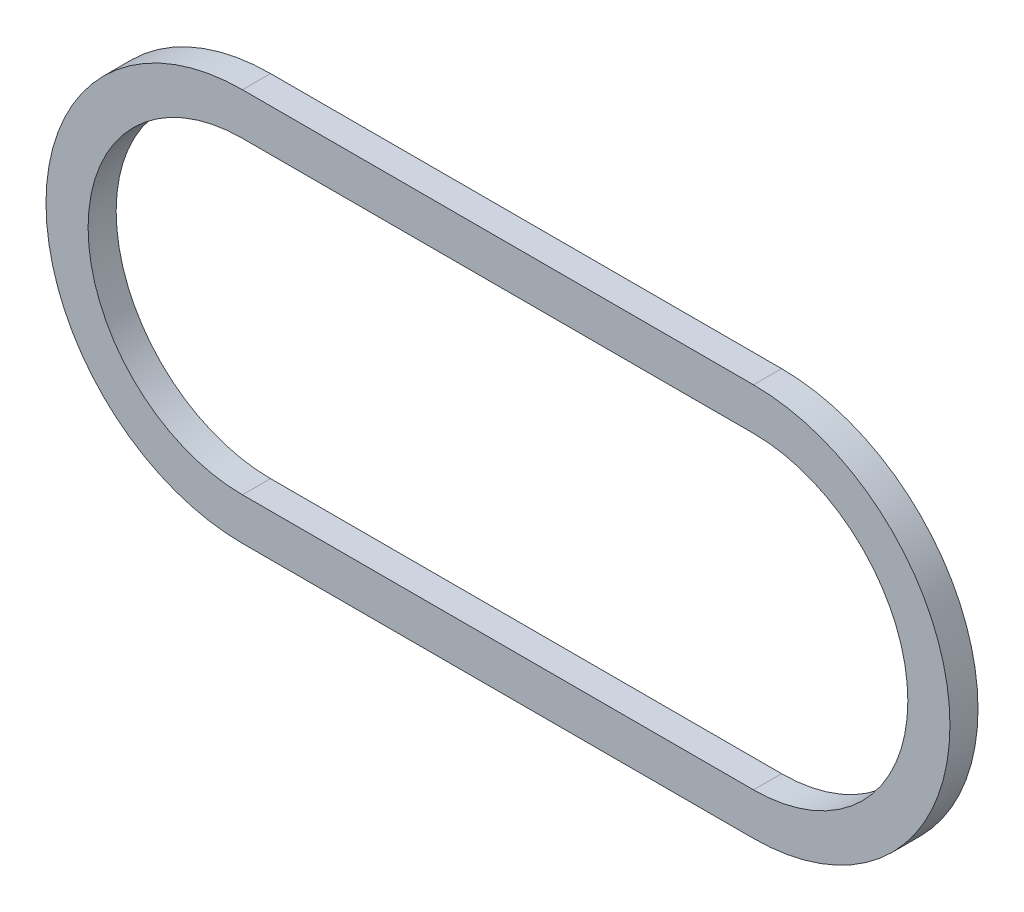
SolidWorks part; units mm, degrees
ref_plane "Front Plane" through (0, 0, 0) normal (0, 0, 1) x (1, 0, 0)
ref_plane "Top Plane" through (0, 0, 0) normal (0, 1, 0) x (1, 0, 0)
ref_plane "Right Plane" through (0, 0, 0) normal (1, 0, 0) x (0, 0, -1)
sketch "Sketch1" plane through (0, 0, 0) normal (0, 0, 1) x (1, 0, 0)
  line L0 (-18.21, 0) -> (18.21, 0) construction
  line L1 (-18.21, 11) -> (18.21, 11)
  line L2 (-18.21, -11) -> (18.21, -11)
  line L3 (-18.21, 14) -> (18.21, 14)
  line L4 (-18.21, -14) -> (18.21, -14)
  arc A0 (-18.21, 11) -> (-18.21, -11) centre (-18.21, 0) ccw
  arc A1 (18.21, -11) -> (18.21, 11) centre (18.21, 0) ccw
  arc A2 (18.21, -14) -> (18.21, 14) centre (18.21, 0) ccw
  arc A3 (-18.21, 14) -> (-18.21, -14) centre (-18.21, 0) ccw
  point P2 (0, 0)
  dimension "D1" = 36.42
  dimension "D2" = 11
  dimension "D3" = 3
extrude "Boss-Extrude1" add sketch "Sketch1" along normal blind 2
